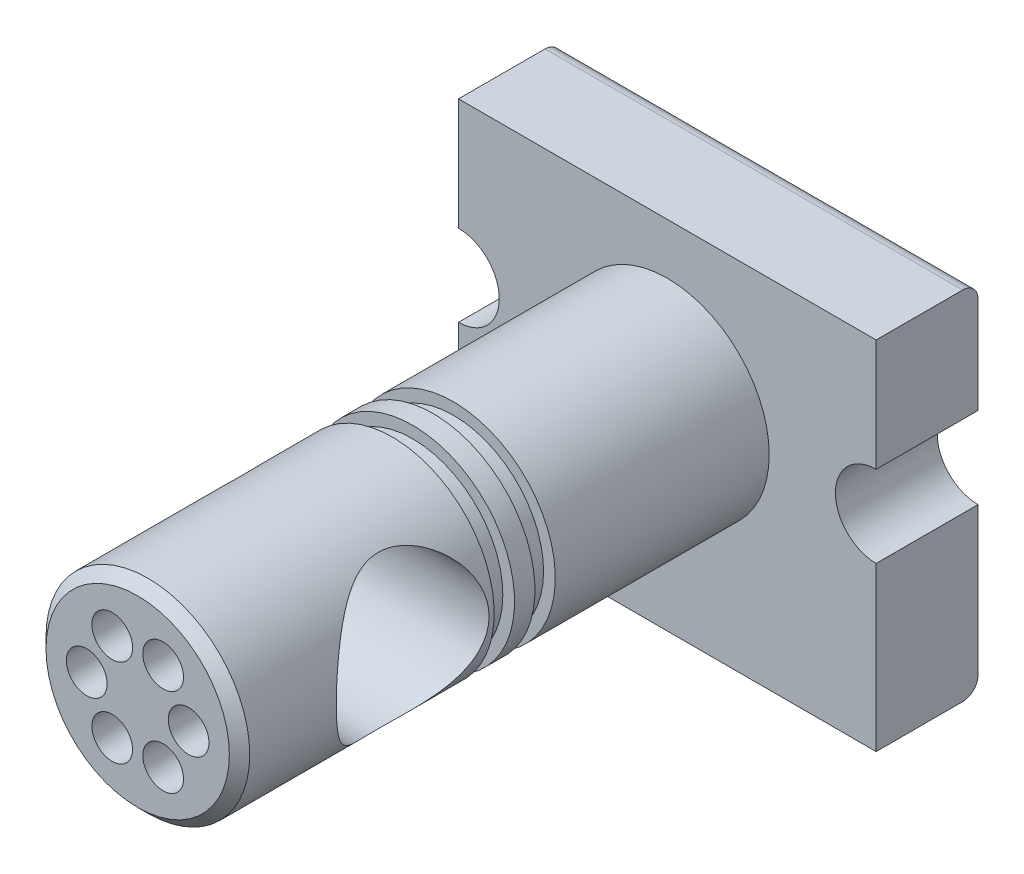
SolidWorks part; units mm, degrees
ref_plane "Front Plane" through (0, 0, 0) normal (0, 0, 1) x (1, 0, 0)
ref_plane "Top Plane" through (0, 0, 0) normal (0, 1, 0) x (1, 0, 0)
ref_plane "Right Plane" through (0, 0, 0) normal (1, 0, 0) x (0, 0, -1)
sketch "Sketch1" plane through (0, 0, 0) normal (0, 0, 1) x (1, 0, 0)
  line L1 (-41, 30) -> (41, 30)
  line L2 (-41, 30) -> (-41, -40)
  line L3 (-41, -40) -> (41, -40)
  line L4 (41, 30) -> (41, -40)
  line L5 (-41, 30) -> (41, -40) construction
  line L6 (-41, -40) -> (41, 30) construction
  point P0 (0, -5)
  dimension "D1" = 70
  dimension "D2" = 82
  dimension "D3" = 40
  dimension "D4" = 41
extrude "Boss-Extrude1" add sketch "Sketch1" along normal blind 20
sketch "Sketch2" plane through (0, 0, 20) normal (0, 0, 1) x (1, 0, 0)
  line L0 (-41, 30) -> (-41, -40) construction
  line L1 (41, -40) -> (41, 30) construction
  line L2 (-41, -40) -> (41, -40) construction
  circle A0 centre (-41, 0) radius 8
  circle A1 centre (41, 0) radius 8
  dimension "D1" = 16
  dimension "D2" = 40
extrude "Cut-Extrude1" cut sketch "Sketch2" against normal blind 20
sketch "Sketch3" plane through (0, 0, 20) normal (0, 0, 1) x (1, 0, 0)
  circle A0 centre (0, 0) radius 20
  dimension "D1" = 40
extrude "Boss-Extrude2" add sketch "Sketch3" along normal blind 104
sketch "Sketch4" plane through (0, 0, 0) normal (1, 0, 0) x (0, 0, -1)
  line L0 (-20, 8) -> (-20, 30) construction
  circle A0 centre (-90, 0) radius 15
  dimension "D2" = 30
  dimension "D1" = 70
extrude "Cut-Extrude2" cut sketch "Sketch4" against normal through all both and the other way through all
sketch "Sketch5" plane through (0, 0, 0) normal (0, 1, 0) x (1, 0, 0)
  line L0 (0, -20) -> (0, -73.2092) construction
  line L1 (-41, -20) -> (41, -20) construction
  line L2 (20, -75) -> (20, -20) construction
  line L3 (20, -74) -> (17.7, -74)
  line L4 (20, -74) -> (20, -70)
  line L5 (20, -70) -> (17.7, -70)
  line L6 (17.7, -74) -> (17.7, -70)
  line L8 (20, -66) -> (17.7, -66)
  line L9 (20, -66) -> (20, -62)
  line L10 (20, -62) -> (17.7, -62)
  line L11 (17.7, -66) -> (17.7, -62)
  dimension "D1" = 4
  dimension "D2" = 4
  dimension "D3" = 4
  dimension "D4" = 42
  dimension "D5" = 2.3
revolve "Cut-Revolve1" cut sketch "Sketch5" angle 360 about L0
sketch "Sketch6" plane through (0, 0, 124) normal (0, 0, 1) x (1, 0, 0)
  circle A0 centre (0, 0) radius 10 construction
  circle A1 centre (-10, 0) radius 4
  dimension "D1" = 20
  dimension "D2" = 8
extrude "Cut-Extrude3" cut sketch "Sketch6" against normal blind 30
pattern_circular "CirPattern1" count 6 over 360 about axis through (0, 0, 0) along (0, 0, 1) of "Cut-Extrude3"
chamfer "Chamfer1" distance 2 1 edges at (20, 0, 124)
fillet "Fillet1" radius 3 2 edges at (0, -40, 0) (0, 30, 0)
